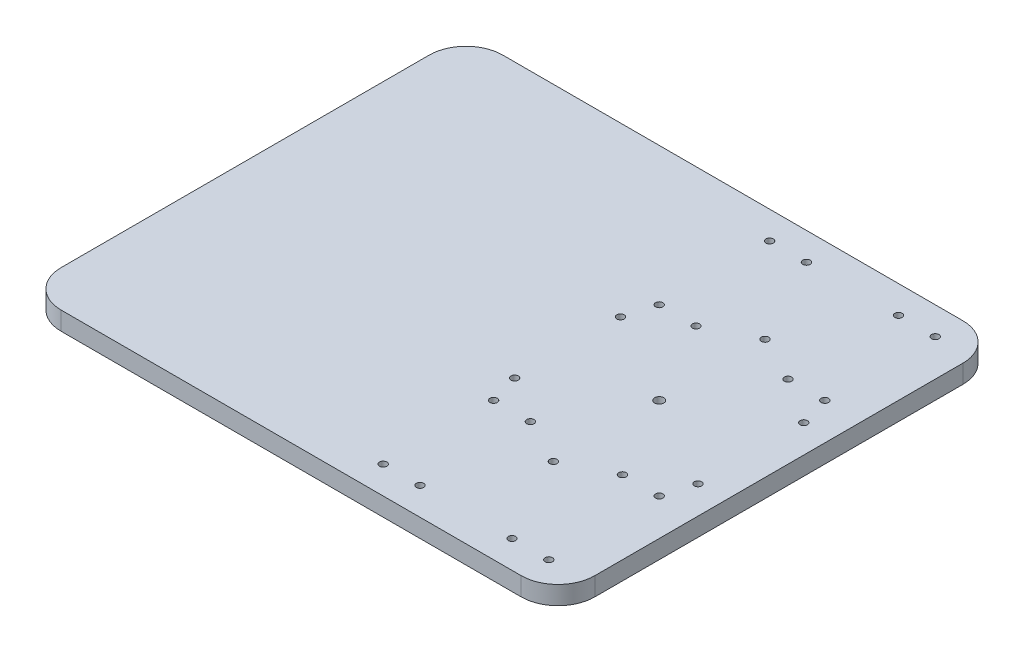
SolidWorks part; units mm, degrees
material "Acrylic (Medium-high impact)"
ref_plane "Front Plane" through (0, 0, 0) normal (0, 0, 1) x (1, 0, 0)
ref_plane "Top Plane" through (0, 0, 0) normal (0, 1, 0) x (1, 0, 0)
ref_plane "Right Plane" through (0, 0, 0) normal (1, 0, 0) x (0, 0, -1)
sketch "Sketch1" plane through (0, 0, 0) normal (0, 1, 0) x (1, 0, 0)
  line L0 (-205, 120) -> (45, 120)
  line L1 (65, 100) -> (65, -100)
  line L2 (45, -120) -> (-205, -120)
  line L3 (-225, -100) -> (-225, 100)
  line L4 (-288.3109, 0) -> (230.4751, 0) construction
  line L5 (0, -162.7992) -> (0, 177.1011) construction
  line L6 (-67.0966, 105) -> (59.4137, 105) construction
  line L7 (-50, 80) -> (50, 80) construction
  line L8 (-50, 80) -> (-50, 70) construction
  line L9 (-50, 70) -> (50, 70) construction
  line L10 (50, 80) -> (50, 70) construction
  line L11 (-50, 80) -> (50, 70) construction
  line L12 (-50, 70) -> (50, 80) construction
  line L13 (-72.1253, 45) -> (63.119, 45) construction
  line L14 (-45, 115.6016) -> (-45, 17.9398) construction
  line L15 (-25, 115.6016) -> (-25, 16.0872) construction
  line L16 (25, 115.6016) -> (25, 16.0872) construction
  line L17 (45, 112.6903) -> (45, 20.0572) construction
  circle A0 centre (0, 0) radius 67.5 construction
  arc A1 (-205, 120) -> (-225, 100) centre (-205, 100) ccw
  arc A2 (-205, -120) -> (-225, -100) centre (-205, -100) cw
  arc A3 (65, 100) -> (45, 120) centre (45, 100) ccw
  arc A4 (65, -100) -> (45, -120) centre (45, -100) cw
  circle A5 centre (0, 0) radius 57.5 construction
  circle A6 centre (0, -57.5) radius 2
  circle A7 centre (-49.7965, -28.75) radius 2
  circle A8 centre (-49.7965, 28.75) radius 2
  circle A9 centre (0, 57.5) radius 2
  circle A10 centre (49.7965, 28.75) radius 2
  circle A11 centre (49.7965, -28.75) radius 2
  circle A12 centre (0, 0) radius 2.5
  circle A13 centre (-45, 105) radius 2
  circle A14 centre (-25, 105) radius 2
  circle A15 centre (25, 105) radius 2
  circle A16 centre (45, 105) radius 2
  circle A17 centre (-45, 45) radius 2
  circle A18 centre (-25, 45) radius 2
  circle A19 centre (25, 45) radius 2
  circle A20 centre (45, 45) radius 2
  circle A21 centre (-45, -45) radius 2
  circle A22 centre (-25, -45) radius 2
  circle A23 centre (25, -45) radius 2
  circle A24 centre (45, -45) radius 2
  circle A25 centre (45, -105) radius 2
  circle A26 centre (25, -105) radius 2
  circle A27 centre (-25, -105) radius 2
  circle A28 centre (-45, -105) radius 2
  point P22 (0, 75)
  point P34 (0, 0)
  point P51 (50, 75)
  dimension "D1" = 135
  dimension "D6" = 20
  dimension "D7" = 20
  dimension "D8" = 20
  dimension "D9" = 20
  dimension "D10" = 115
  dimension "D11" = 4
  dimension "D13" = 5
  dimension "D23" = 4
  dimension "D24" = 4
  dimension "D25" = 4
  dimension "D26" = 4
  dimension "D27" = 4
  dimension "D28" = 4
  dimension "D29" = 4
  dimension "D30" = 4
  dimension "D2" = 120
  dimension "D3" = 120
  dimension "D4" = 65
  dimension "D5" = 225
  dimension "D14" = 100
  dimension "D15" = 10
  dimension "D16" = 70
  dimension "D17" = 5
  dimension "D18" = 5
  dimension "D19" = 20
  dimension "D20" = 20
  dimension "D21" = 25
  dimension "D22" = 25
  dimension "D12" = 6
extrude "Boss-Extrude1" add sketch "Sketch1" along normal blind 10
